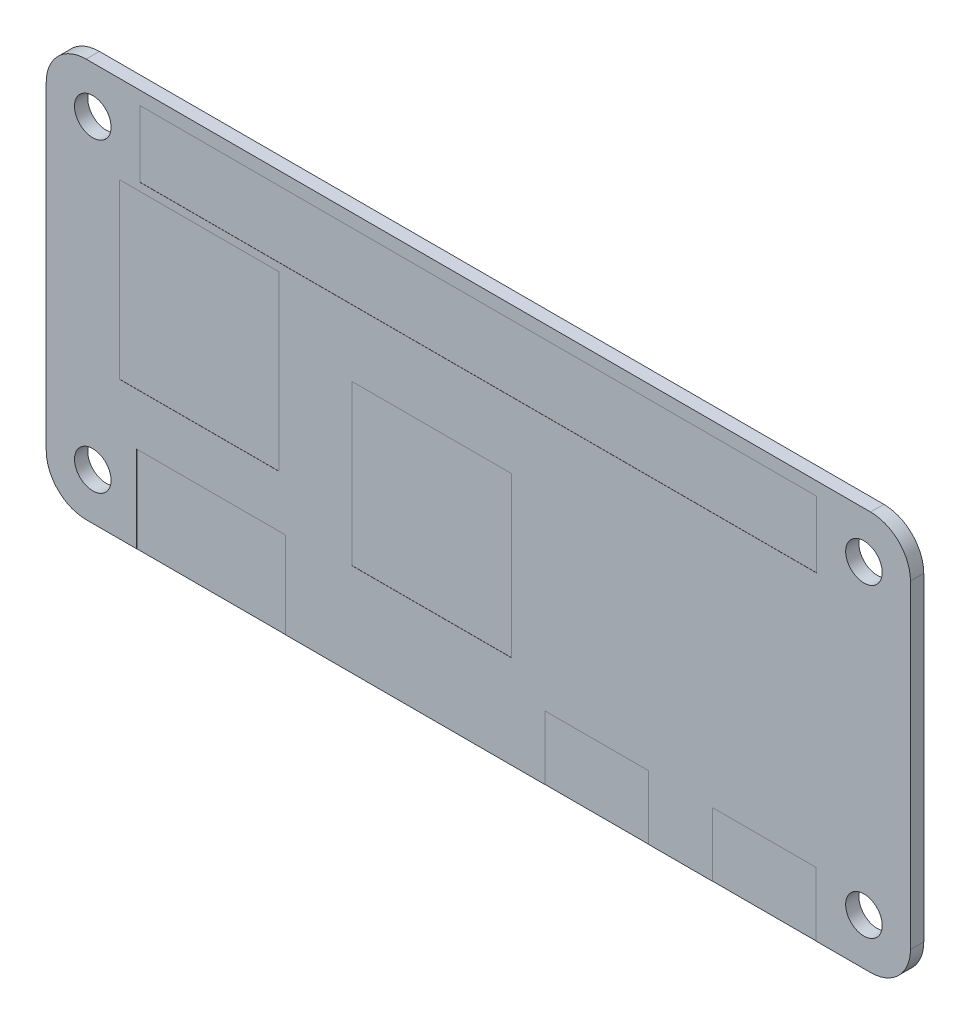
SolidWorks part; units mm, degrees
ref_plane "Plan de face" through (0, 0, 0) normal (0, 0, 1) x (1, 0, 0)
ref_plane "Plan de dessus" through (0, 0, 0) normal (0, 1, 0) x (1, 0, 0)
ref_plane "Plan de droite" through (0, 0, 0) normal (1, 0, 0) x (0, 0, -1)
sketch "Sketch1" plane through (0, 0, 0) normal (0, 0, 1) x (1, 0, 0)
  line L1 (29.5, -15) -> (-29.5, -15)
  line L2 (32.5, -12) -> (32.5, 12)
  line L3 (29.5, 15) -> (-29.5, 15)
  line L4 (-32.5, -12) -> (-32.5, 12)
  line L5 (32.5, -15) -> (-32.5, 15) construction
  line L6 (32.5, 15) -> (-32.5, -15) construction
  circle A0 centre (-29, 11.5) radius 1.375
  circle A1 centre (-29, -11.5) radius 1.375
  circle A2 centre (29, -11.5) radius 1.375
  circle A3 centre (29, 11.5) radius 1.375
  arc A4 (32.5, 12) -> (29.5, 15) centre (29.5, 12) ccw
  arc A5 (29.5, -15) -> (32.5, -12) centre (29.5, -12) ccw
  arc A6 (-29.5, -15) -> (-32.5, -12) centre (-29.5, -12) cw
  arc A7 (-29.5, 15) -> (-32.5, 12) centre (-29.5, 12) ccw
  point P0 (0, 0)
  dimension "D5" = 2.75
  dimension "D8" = 3
  dimension "D1" = 65
  dimension "D2" = 30
  dimension "D3" = 3.5
  dimension "D4" = 3.5
  dimension "D6" = 3.5
  dimension "D7" = 3.5
extrude "Boss-Extrude1" add sketch "Sketch1" along normal blind 1
sketch "Sketch2" plane through (0, 0, 1) normal (0, 0, 1) x (1, 0, 0)
  line L0 (-29, 11.5) -> (-35.8933, 11.5) construction
  line L1 (-25.45, 9) -> (25.45, 9)
  line L2 (-25.45, 9) -> (-25.45, 14)
  line L3 (-25.45, 14) -> (25.45, 14)
  line L4 (25.45, 9) -> (25.45, 14)
  line L5 (-25.45, 9) -> (25.45, 14) construction
  line L6 (-25.45, 14) -> (25.45, 9) construction
  line L7 (-29.5, -15) -> (29.5, -15) construction
  line L8 (17.6, -10.2) -> (25.4, -10.2)
  line L9 (17.6, -10.2) -> (17.6, -15)
  line L10 (17.6, -15) -> (25.4, -15)
  line L11 (25.4, -10.2) -> (25.4, -15)
  line L12 (17.6, -10.2) -> (25.4, -15) construction
  line L13 (17.6, -15) -> (25.4, -10.2) construction
  line L14 (5, -10.2) -> (12.8, -10.2)
  line L15 (5, -10.2) -> (5, -15)
  line L16 (5, -15) -> (12.8, -15)
  line L17 (12.8, -10.2) -> (12.8, -15)
  line L18 (5, -10.2) -> (12.8, -15) construction
  line L19 (5, -15) -> (12.8, -10.2) construction
  line L20 (-32.5, 12) -> (-32.5, -12) construction
  line L22 (32.5, -12) -> (32.5, 12) construction
  line L23 (-25.7, -8.5) -> (-14.5, -8.5)
  line L24 (-25.7, -8.5) -> (-25.7, -15)
  line L25 (-25.7, -15) -> (-14.5, -15)
  line L26 (-14.5, -8.5) -> (-14.5, -15)
  line L27 (-25.7, -8.5) -> (-14.5, -15) construction
  line L28 (-25.7, -15) -> (-14.5, -8.5) construction
  line L29 (-27, 8.4) -> (-15, 8.4)
  line L30 (-27, 8.4) -> (-27, -4.6)
  line L31 (-27, -4.6) -> (-15, -4.6)
  line L32 (-15, 8.4) -> (-15, -4.6)
  line L33 (-27, 8.4) -> (-15, -4.6) construction
  line L34 (-27, -4.6) -> (-15, 8.4) construction
  line L35 (-9.5, -8) -> (2.5, -8)
  line L36 (-9.5, -8) -> (-9.5, 4)
  line L37 (-9.5, 4) -> (2.5, 4)
  line L38 (2.5, -8) -> (2.5, 4)
  line L39 (-9.5, -8) -> (2.5, 4) construction
  line L40 (-9.5, 4) -> (2.5, -8) construction
  line L41 (29.5, 15) -> (-29.5, 15) construction
  point P0 (0, 11.5)
  point P8 (21.5, -12.6)
  point P14 (8.9, -12.6)
  point P23 (-20.1, -11.75)
  point P28 (-21, 1.9)
  point P33 (-3.5, -2)
  dimension "D1" = 50.9
  dimension "D2" = 5
  dimension "D3" = 7.8
  dimension "D4" = 4.8
  dimension "D5" = 54
  dimension "D6" = 41.4
  dimension "D7" = 13
  dimension "D8" = 12.4
  dimension "D9" = 12
  dimension "D10" = 16.9
  dimension "D11" = 11.2
  dimension "D12" = 6.5
  dimension "D13" = 17.5
  dimension "D14" = 12
  dimension "D15" = 30
  dimension "D16" = 11
extrude "Cut-Extrude1" cut sketch "Sketch2" against normal blind 0.01
equation "\"D6@Sketch1\"=\"D4@Sketch1\""
equation "\"D7@Sketch1\"=\"D3@Sketch1\""
